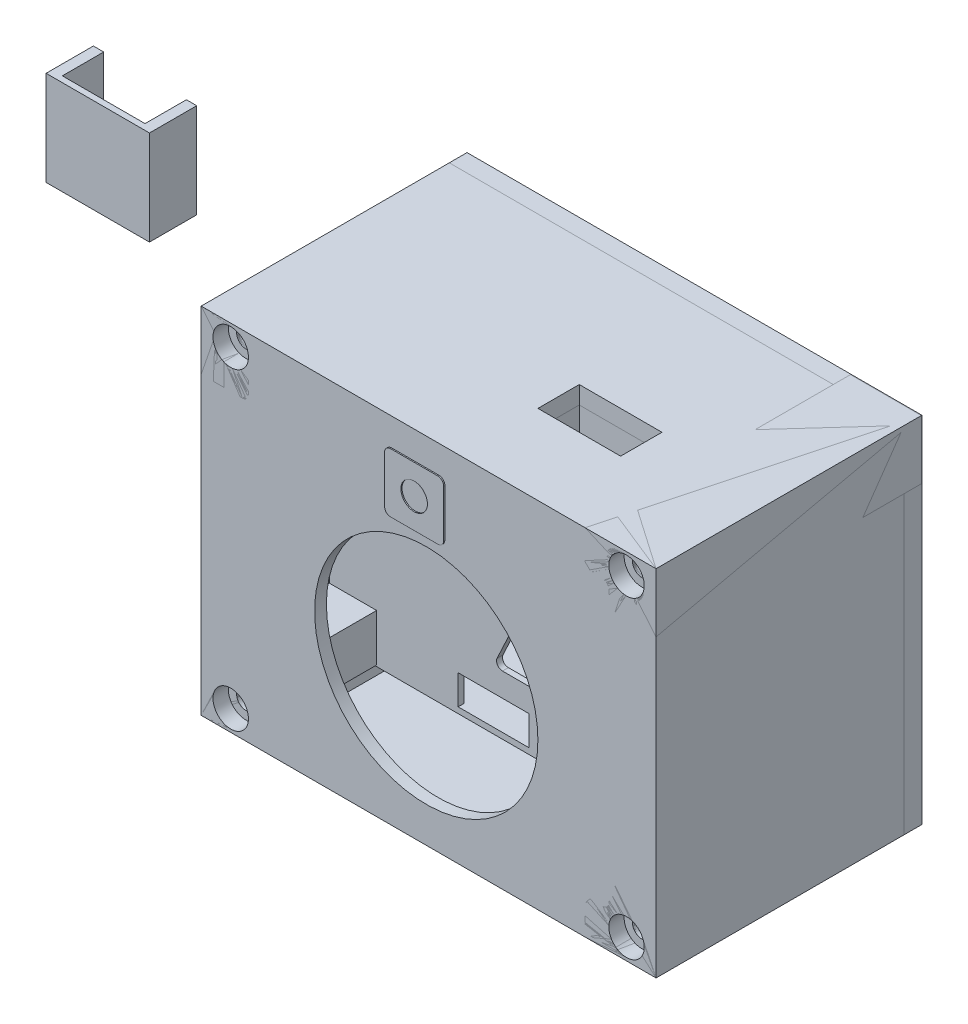
SolidWorks part; units mm, degrees
ref_plane "Front Plane" through (0, 0, 0) normal (0, 0, 1) x (1, 0, 0)
ref_plane "Top Plane" through (0, 0, 0) normal (0, 1, 0) x (1, 0, 0)
ref_plane "Right Plane" through (0, 0, 0) normal (1, 0, 0) x (0, 0, -1)
sketch "NodeBaseSection" plane through (0, 0, 0) normal (0, 0, 1) x (1, 0, 0)
  line L1 (0, 0) -> (-48.4, 0)
  line L2 (0, 0) -> (0, 25.7)
  line L3 (0, 25.7) -> (-48.4, 25.7)
  line L4 (-48.4, 0) -> (-48.4, 25.7)
  dimension "D1" = 48.4
  dimension "D2" = 25.7
sketch "WiFiModemSection" plane through (0, 0, 0) normal (0, 0, 1) x (1, 0, 0)
  line L1 (-7.6, 6.85) -> (-22.6, 6.85)
  line L2 (-7.6, 6.85) -> (-7.6, 18.85)
  line L3 (-7.6, 18.85) -> (-22.6, 18.85)
  line L4 (-22.6, 6.85) -> (-22.6, 18.85)
  line L5 (-49.2, 16.55) -> (-43.5, 16.55)
  line L6 (-49.2, 16.55) -> (-49.2, 9.15)
  line L7 (-49.2, 9.15) -> (-43.5, 9.15)
  line L8 (-43.5, 16.55) -> (-43.5, 9.15)
  dimension "D1" = 15
  dimension "D2" = 12
  dimension "D3" = 7.6
  dimension "D4" = 6.85
  dimension "D5" = 7.4
  dimension "D6" = 5.7
  dimension "D7" = 9.15
  dimension "D8" = 43.5
extrude "NodeBase" add sketch "NodeBaseSection" along normal blind 1.7 contours L3 L4 L1 L2
extrude "MicroPort+WiFiModem" add sketch "WiFiModemSection" along normal blind 2.7
sketch "AntennaSection" plane through (0, 0, 1.7) normal (0, 0, 1) x (1, 0, 0)
  line L0 (-6.6, 7.8) -> (-6.6, 18.2)
  line L1 (-6.6, 18.2) -> (-0.8, 18.2)
  line L2 (-0.8, 18.2) -> (-0.8, 15.8)
  line L3 (-0.8, 15.8) -> (-4.442, 15.8)
  line L4 (-4.442, 15.8) -> (-4.442, 15)
  line L5 (-4.442, 15) -> (-0.8, 15)
  line L6 (-0.8, 15) -> (-0.8, 12.6)
  line L7 (-0.8, 12.6) -> (-4.442, 12.6)
  line L8 (-4.442, 12.6) -> (-4.442, 11.8)
  line L9 (-4.442, 11.8) -> (-0.8, 11.8)
  line L10 (-0.8, 11.8) -> (-0.8, 9.4)
  line L11 (-0.8, 9.4) -> (-4.442, 9.4)
  line L12 (-4.442, 9.4) -> (-4.442, 8.6)
  line L13 (-4.442, 8.6) -> (-0.8, 8.6)
  line L14 (-0.8, 8.6) -> (-0.8, 4.6)
  line L15 (-0.8, 4.6) -> (-1.6, 4.6)
  line L16 (-1.6, 4.6) -> (-1.6, 7.8)
  line L17 (-1.6, 7.8) -> (-5.242, 7.8)
  line L18 (-5.242, 7.8) -> (-5.242, 10.2)
  line L19 (-5.242, 10.2) -> (-1.6, 10.2)
  line L20 (-1.6, 10.2) -> (-1.6, 11)
  line L21 (-1.6, 11) -> (-5.242, 11)
  line L22 (-5.242, 11) -> (-5.242, 13.4)
  line L23 (-5.242, 13.4) -> (-1.6, 13.4)
  line L24 (-1.6, 13.4) -> (-1.6, 14.2)
  line L25 (-1.6, 14.2) -> (-5.242, 14.2)
  line L26 (-5.242, 14.2) -> (-5.242, 16.6)
  line L27 (-5.242, 16.6) -> (-1.6, 16.6)
  line L28 (-1.6, 16.6) -> (-1.6, 17.4)
  line L29 (-1.6, 17.4) -> (-5.8, 17.4)
  line L30 (-5.8, 17.4) -> (-5.8, 7.8)
  line L31 (-5.8, 7.8) -> (-6.6, 7.8)
  dimension "D1" = 0.8
  dimension "D2" = 0.8
  dimension "D3" = 0.8
  dimension "D4" = 0.8
  dimension "D5" = 0.8
  dimension "D6" = 0.8
  dimension "D7" = 0.8
  dimension "D8" = 0.8
  dimension "D9" = 0.8
  dimension "D10" = 0.8
  dimension "D11" = 0.8
  dimension "D12" = 0.8
  dimension "D13" = 0.8
  dimension "D14" = 0.8
  dimension "D15" = 0.8
  dimension "D16" = 0.8
  dimension "D17" = 0.8
  dimension "D18" = 0.8
  dimension "D19" = 0.8
  dimension "D20" = 3.2
extrude "Antenna" add sketch "AntennaSection" along normal blind 0.2
move or copy body "MovedWholeNode" bodies to move or copy 112 copy no translate (72.4, -2.35, 0)
sketch "4NodeAttachmentHolesSection" plane through (0, 0, 0) normal (0, 0, -1) x (-1, 0, 0)
  line L0 (-72.4, -2.35) -> (-24, -2.35) construction
  circle A0 centre (-69.9, 0.05) radius 1.5
  circle A1 centre (-69.9, 20.95) radius 1.5
  circle A2 centre (-26.1, 20.95) radius 1.5
  circle A3 centre (-26.1, 0.05) radius 1.5
  dimension "D1" = 3
  dimension "D2" = 3
  dimension "D3" = 3
  dimension "D4" = 3
  dimension "D5" = 43.8
  dimension "D6" = 20.9
  dimension "D7" = 2.4
  dimension "D8" = 43.8
  dimension "D9" = 26.1
extrude "4NodeAttachmentHoles" cut sketch "4NodeAttachmentHolesSection" against normal blind 2
sketch "DSMBluePinsSection" plane through (0, 0, 0) normal (0, 0, 1) x (1, 0, 0)
  line L5 (-20.5, 43.05) -> (-14.5, 43.05)
  line L6 (-20.5, 43.05) -> (-20.5, 37.05)
  line L7 (-20.5, 37.05) -> (-14.5, 37.05)
  line L8 (-14.5, 43.05) -> (-14.5, 37.05)
  line L9 (-10.5, 43.05) -> (-4.5, 43.05)
  line L10 (-10.5, 43.05) -> (-10.5, 37.05)
  line L11 (-10.5, 37.05) -> (-4.5, 37.05)
  line L12 (-4.5, 43.05) -> (-4.5, 37.05)
  dimension "D3" = 6
  dimension "D4" = 6
  dimension "D5" = 6
extrude "DSMBluePins" add sketch "DSMBluePinsSection" along normal blind 5 contours L8 L7 L6 L5 | L11 L12 L9 L10
sketch "PCBSection" plane through (0, 0, 0) normal (0, 0, 1) x (1, 0, 0)
  line L1 (0, 0) -> (-58.8, 0)
  line L2 (0, 0) -> (0, 44.55)
  line L3 (0, 44.55) -> (-58.8, 44.55)
  line L4 (-58.8, 0) -> (-58.8, 44.55)
  dimension "D1" = 58.8
  dimension "D2" = 44.55
extrude "PCB" add sketch "PCBSection" against normal blind 1.5
sketch "BlackPlasticCoverSection" plane through (0, 0, 0) normal (0, 0, 1) x (1, 0, 0)
  line L0 (-58.8, 44.55) -> (-58.8, 0) construction
  line L5 (0, 1) -> (-58.8, 1)
  line L8 (-58.8, 1) -> (-58.8, 36.5)
  line L9 (0, -1.485) -> (0, 1.485) construction
  line L10 (0, 36.5) -> (-36.6, 36.5)
  line L11 (-36.6, 36.5) -> (-50.5, 43.3)
  line L12 (-50.5, 43.3) -> (-58.8, 36.5)
  line L13 (0, 7) -> (0, 1)
  line L14 (0, 7) -> (-2, 7)
  line L15 (-2, 7) -> (-2, 8)
  line L16 (-2, 8) -> (-4.5, 8)
  line L17 (-4.5, 8) -> (-4.5, 13)
  line L18 (-4.5, 13) -> (0, 13)
  line L19 (0, 13) -> (0, 36.5)
  dimension "D1" = 1
  dimension "D2" = 36.5
  dimension "D3" = 2
  dimension "D4" = 1
  dimension "D5" = 2.5
  dimension "D6" = 5
extrude "BlackPlasticCover" add sketch "BlackPlasticCoverSection" along normal blind 15 separate body
sketch "3HolesCutterSection" plane through (0, 0, 15) normal (0, 0, 1) x (1, 0, 0)
  line L0 (-6.5, 17) -> (-11.6962, 14)
  line L1 (-25, 2) -> (-37, 2)
  line L2 (-25, 2) -> (-25, 7)
  line L3 (-25, 7) -> (-37, 7)
  line L4 (-37, 2) -> (-37, 7)
  line L5 (-11.6962, 14) -> (-13.9462, 17.8971)
  line L6 (-13.9462, 17.8971) -> (-8.75, 20.8971)
  line L7 (-8.75, 20.8971) -> (-6.5, 17)
  line L8 (-21, 11) -> (-29.5, 11)
  line L9 (-30.4061, 12.4231) -> (-24.9061, 24.2023)
  line L10 (-24, 24.7792) -> (-21, 24.7792)
  line L11 (-20, 23.7792) -> (-20, 12)
  line L12 (21.45, 0) -> (-21.45, 0) construction
  arc A0 (-29.5, 11) -> (-30.4061, 12.4231) centre (-29.5, 12) cw
  arc A1 (-24.9061, 24.2023) -> (-24, 24.7792) centre (-24, 23.7792) cw
  arc A2 (-21, 24.7792) -> (-20, 23.7792) centre (-21, 23.7792) cw
  arc A3 (-21, 11) -> (-20, 12) centre (-21, 12) ccw
  dimension "D5" = 1
  dimension "D7" = 3
  dimension "D1" = 12
  dimension "D2" = 5
  dimension "D3" = 6
  dimension "D4" = 4.5
  dimension "D6" = 8.5
  dimension "D8" = 13
  dimension "D9" = 30
  dimension "D10" = 6.5
  dimension "D11" = 17
  dimension "D12" = 25
  dimension "D13" = 2
  dimension "D14" = 20
  dimension "D15" = 11
sketch "HoleCutterSection" [suppressed] plane through (0, 0, 0) normal (0, 0, 1) x (1, 0, 0)
  circle A0 centre (-31.75, 41.1) radius 2.25
  dimension "D1" = 4.5
  dimension "D2" = 27.05
extrude "HoleCutter" [suppressed] cut sketch "HoleCutterSection" against normal blind 3.2
shell "BlackDSMShell" thickness 1
sketch "SideHoleCutterSection" plane through (0, 36.5, 0) normal (0, 1, 0) x (1, 0, 0)
  line L1 (-10.5, -14) -> (-24.5, -14)
  line L2 (-10.5, -14) -> (-10.5, -7)
  line L3 (-10.5, -7) -> (-24.5, -7)
  line L4 (-24.5, -14) -> (-24.5, -7)
  dimension "D1" = 7
  dimension "D2" = 14
  dimension "D3" = 10.5
  dimension "D4" = 14
extrude "SideHoleCutter" cut sketch "SideHoleCutterSection" against normal blind 1.5 contours L1 L4 L3 L2
extrude "3HolesCutter" cut sketch "3HolesCutterSection" against normal blind 1.5
sketch "5PinConnectorHoleCutterSection" [suppressed] plane through (0, 1, 0) normal (0, -1, 0) x (1, 0, 0)
  line L1 (-57.8, 0) -> (-37.8, 0)
  line L2 (-57.8, 0) -> (-57.8, 11)
  line L3 (-57.8, 11) -> (-37.8, 11)
  line L4 (-37.8, 0) -> (-37.8, 11)
  line L6 (-58.8, 15) -> (-58.8, 0) construction
  dimension "D1" = 11
  dimension "D2" = 20
  dimension "D3" = 1
  dimension "D4" = 0
extrude "5PinConnectorHoleCutter" [suppressed] cut sketch "5PinConnectorHoleCutterSection" against normal blind 1.5
sketch "5PinConnectorSection" [suppressed] plane through (0, 0, 0) normal (0, 0, 1) x (1, 0, 0)
  line L1 (-54.7, 15.6) -> (-42.7, 15.6)
  line L2 (-54.7, 15.6) -> (-54.7, 2.6)
  line L3 (-54.7, 2.6) -> (-42.7, 2.6)
  line L4 (-42.7, 15.6) -> (-42.7, 2.6)
  dimension "D1" = 12
  dimension "D2" = 13
extrude "5PinConnector" [suppressed] add sketch "5PinConnectorSection" along normal blind 5 contours L1 L4 L3 L2
shell "WhiteConnectorShell" [suppressed] thickness 0.5
sketch "BoxCapSection(ToNode)" plane through (0, 0, 0) normal (0, 0, 1) x (1, 0, 0)
  line L1 (21, -19.5) -> (98, -19.5)
  line L2 (21, -19.5) -> (21, 40.5)
  line L3 (21, 40.5) -> (98, 40.5)
  line L4 (98, -19.5) -> (98, 40.5)
  line L5 (-14.8, 82.1) -> (62.2, 82.1) construction
  line L6 (-14.8, 82.1) -> (-14.8, 132.1) construction
  line L7 (-14.8, 132.1) -> (62.2, 132.1) construction
  line L8 (62.2, 82.1) -> (62.2, 132.1) construction
  circle A0 centre (-9.8, 127.1) radius 1.5
  circle A1 centre (57.2, 87.1) radius 1.5
  dimension "D6" = 3
  dimension "D7" = 3
  dimension "D1" = 60
  dimension "D2" = 77
  dimension "D3" = 50
  dimension "D5" = 77
  dimension "D8" = 5
  dimension "D9" = 5
  dimension "D10" = 5
  dimension "D11" = 5
extrude "BoxCap(ToNode)" add sketch "BoxCapSection(ToNode)" along normal blind 3 from offset 9 separate body contours L1 L4 L3 L2 offset against normal yes
sketch "NodeScrewColumnsSection" plane through (0, 0, -6) normal (0, 0, 1) x (1, 0, 0)
  line L1 (64.4, -2.15) -> (72.4, -2.15)
  line L2 (64.4, -2.15) -> (64.4, 5.85)
  line L3 (64.4, 5.85) -> (72.4, 5.85)
  line L4 (72.4, -2.15) -> (72.4, 5.85)
  line L28 (24, -2.15) -> (32, -2.15)
  line L29 (24, -2.15) -> (24, 5.85)
  line L30 (24, 5.85) -> (32, 5.85)
  line L31 (32, -2.15) -> (32, 5.85)
  line L32 (24, 15) -> (32, 15)
  line L33 (24, 15) -> (24, 23)
  line L34 (24, 23) -> (32, 23)
  line L35 (32, 15) -> (32, 23)
  line L36 (64.4, 15) -> (72.4, 15)
  line L37 (64.4, 15) -> (64.4, 23)
  line L38 (64.4, 23) -> (72.4, 23)
  line L39 (72.4, 15) -> (72.4, 23)
  dimension "D1" = 8
  dimension "D2" = 8
  dimension "D3" = 8
  dimension "D4" = 8
  dimension "D5" = 8
  dimension "D6" = 8
  dimension "D7" = 8
  dimension "D8" = 8
  dimension "D9" = 24
  dimension "D10" = 2.15
  dimension "D11" = 24
  dimension "D12" = 15
  dimension "D13" = 72.4
  dimension "D14" = 2.15
  dimension "D15" = 72.4
  dimension "D16" = 15
extrude "NodeScrewColumns" add sketch "NodeScrewColumnsSection" along normal blind 6
sketch "BoxCapSection(ToDSM)" plane through (0, 0, 0) normal (0, 0, 1) x (1, 0, 0)
  line L0 (21, -19.5) -> (98, -19.5)
  line L1 (21, -19.5) -> (21, 40.5)
  line L2 (21, 40.5) -> (98, 40.5)
  line L3 (98, -19.5) -> (98, 40.5)
  line L4 (-23.4569, 88.0645) -> (53.5431, 88.0645) construction
  line L5 (-23.4569, 88.0645) -> (-23.4569, 138.0645) construction
  line L6 (-23.4569, 138.0645) -> (53.5431, 138.0645) construction
  line L7 (53.5431, 88.0645) -> (53.5431, 138.0645) construction
  circle A0 centre (-18.4569, 133.0645) radius 1.5
  circle A1 centre (48.5431, 93.0645) radius 1.5
  dimension "D1" = 77
  dimension "D2" = 60
extrude "BoxCap(ToDSM)" add sketch "BoxCapSection(ToDSM)" against normal blind 42 from offset 36 separate body contours L0 L3 L2 L1
shell "HollowBoxCap(ToDSM)" thickness 3
sketch "DSMLegsSection" plane through (0, 0, 33) normal (0, 0, -1) x (-1, 0, 0)
  line L1 (-88.9, -9.77) -> (-30.2, -9.77) construction
  line L2 (-88.9, -9.77) -> (-88.9, 25.5) construction
  line L3 (-88.9, 25.5) -> (-30.2, 25.5) construction
  line L4 (-30.2, -9.77) -> (-30.2, 25.5) construction
  line L6 (-24, -16.5) -> (-95, -16.5) construction
  line L7 (-95, -16.5) -> (-95, 37.5) construction
  line L9 (-30.2, -9.77) -> (-38.2, -9.77)
  line L10 (-30.2, -9.77) -> (-30.2, -1.77)
  line L11 (-30.2, -1.77) -> (-38.2, -1.77)
  line L12 (-38.2, -9.77) -> (-38.2, -1.77)
  line L13 (-30.2, 17.5) -> (-38.2, 17.5)
  line L14 (-30.2, 17.5) -> (-30.2, 25.5)
  line L15 (-30.2, 25.5) -> (-38.2, 25.5)
  line L16 (-38.2, 17.5) -> (-38.2, 25.5)
  line L17 (-80.9, -9.77) -> (-88.9, -9.77)
  line L18 (-80.9, -9.77) -> (-80.9, -4.27)
  line L19 (-80.9, -4.27) -> (-88.9, -4.27)
  line L20 (-88.9, -9.77) -> (-88.9, -4.27)
  line L21 (-80.9, 17.5) -> (-88.9, 17.5)
  line L22 (-80.9, 17.5) -> (-80.9, 25.5)
  line L23 (-80.9, 25.5) -> (-88.9, 25.5)
  line L24 (-88.9, 17.5) -> (-88.9, 25.5)
  dimension "D13" = 30.2
  dimension "D2" = 25.5
  dimension "D3" = 6.73
  dimension "D4" = 6.1
  dimension "D5" = 8
  dimension "D6" = 8
  dimension "D7" = 8
  dimension "D8" = 8
  dimension "D9" = 5.5
  dimension "D10" = 8
  dimension "D11" = 8
  dimension "D12" = 8
extrude "DSMLegs" add sketch "DSMLegsSection" along normal blind 9.5
sketch "FanCutterSection" plane through (0, 0, 36) normal (0, 0, 1) x (1, 0, 0)
  circle A4 centre (59.1, 5.4) radius 18.9
  point P12 (79.2, 28.2)
  point P15 (79.2, -12)
  point P18 (39, 28.2)
  dimension "D3" = 59.1
  dimension "D6" = 37.8
  dimension "D1" = 40.2
  dimension "D2" = 40.2
  dimension "D4" = 5.4
sketch "SquareFanBodyCutterSection" plane through (0, 0, 36) normal (0, 0, 1) x (1, 0, 0)
  line L0 (42.1, -14.6) -> (76.1, -14.6)
  line L1 (39.1, -11.6) -> (39.1, 22.4)
  line L2 (42.1, 25.4) -> (76.1, 25.4)
  line L3 (79.1, -11.6) -> (79.1, 22.4)
  line L4 (42.1, -11.6) -> (76.1, 22.4) construction
  line L5 (42.1, 22.4) -> (76.1, -11.6) construction
  arc A0 (42.1, -14.6) -> (39.1, -11.6) centre (42.1, -11.6) cw
  arc A1 (76.1, 25.4) -> (79.1, 22.4) centre (76.1, 22.4) cw
  arc A2 (76.1, -14.6) -> (79.1, -11.6) centre (76.1, -11.6) ccw
  arc A3 (39.1, 22.4) -> (42.1, 25.4) centre (42.1, 22.4) cw
  dimension "D1" = 3
  dimension "D3" = 34
  dimension "D4" = 34
extrude "FanCutter" cut sketch "FanCutterSection" against normal blind 3
extrude "SquareFanBodyCutter" cut sketch "SquareFanBodyCutterSection" against normal blind 3 from offset 2 offset against normal yes
sketch "ExhaustDuctSection" plane through (0, 40.5, 0) normal (0, 1, 0) x (1, 0, 0)
  line L0 (-10.5, -7) -> (-8.75, -7)
  line L1 (-8.75, -7) -> (-8.75, -15)
  line L2 (-8.75, -15) -> (-26.25, -15)
  line L3 (0, -15) -> (-36.6, -15) construction
  line L4 (-26.25, -15) -> (-26.25, -7)
  line L5 (-26.25, -7) -> (-24.5, -7)
  line L6 (-24.5, -7) -> (-24.5, -14)
  line L7 (-24.5, -14) -> (-24.5, -7) construction
  line L8 (-24.5, -14) -> (-10.5, -14)
  line L9 (-10.5, -14) -> (-10.5, -7) construction
  line L10 (-25, -14) -> (-1, -14) construction
  line L11 (-10.5, -14) -> (-10.5, -7)
  dimension "D1" = 1.75
extrude "ExhaustDuct" add sketch "ExhaustDuctSection" against normal blind 16 separate body
sketch "ExhaustHoleCutterSection" plane through (0, 40.5, 0) normal (0, 1, 0) x (1, 0, 0)
  line L1 (78.5, -22.5) -> (64.5, -22.5)
  line L2 (78.5, -22.5) -> (78.5, -15.5)
  line L3 (78.5, -15.5) -> (64.5, -15.5)
  line L4 (64.5, -22.5) -> (64.5, -15.5)
  dimension "D1" = 14
  dimension "D2" = 7
  dimension "D3" = 64.5
  dimension "D4" = 15.5
extrude "ExhaustHoleCutter" cut sketch "ExhaustHoleCutterSection" against normal blind 5
sketch "MicroUSBHoleCutterSection" plane through (21, 0, 0) normal (-1, 0, 0) x (0, 0, 1)
  line L1 (3.6, 16.75) -> (-0.9, 16.75)
  line L2 (4.6, 15.75) -> (4.6, 5.25)
  line L3 (3.6, 4.25) -> (-0.9, 4.25)
  line L4 (-1.9, 15.75) -> (-1.9, 5.25)
  arc A0 (4.6, 5.25) -> (3.6, 4.25) centre (3.6, 5.25) cw
  arc A1 (-0.9, 4.25) -> (-1.9, 5.25) centre (-0.9, 5.25) cw
  arc A2 (-0.9, 16.75) -> (-1.9, 15.75) centre (-0.9, 15.75) ccw
  arc A3 (3.6, 16.75) -> (4.6, 15.75) centre (3.6, 15.75) cw
  point P10 (4.6, 4.25)
  point P13 (-1.9, 4.25)
  point P18 (4.6, 16.75)
  dimension "D5" = 1
  dimension "D1" = 12.5
  dimension "D2" = 6.5
  dimension "D3" = 4.25
  dimension "D4" = 4.6
move or copy body "DSMModule" bodies to move or copy 116 106 copy no translate (89, -11, 8.5)
sketch "ScrewDSMHoleCutterSection" plane through (0, 0, 8.5) normal (0, 0, 1) x (1, 0, 0)
  line L0 (30.2, 33.55) -> (30.2, -11) construction
  circle A0 centre (57.25, 30.825) radius 2.25
  dimension "D2" = 4.5
  dimension "D1" = 27.05
  dimension "D3" = 30.825
extrude "ScrewDSMHoleCutter" cut sketch "ScrewDSMHoleCutterSection" against normal blind 2
extrude "MicroUSBHoleCutter" cut sketch "MicroUSBHoleCutterSection" against normal blind 3 contours L3 A1 L4 A2 L1 A3 L2 A0
sketch "ExhaustHoleDuctSection" plane through (0, 25.5, 0) normal (0, 1, 0) x (1, 0, 0)
  line L16 (79.5, -23.5) -> (63.5, -23.5)
  line L17 (78.5, -22.5) -> (64.5, -22.5)
  line L18 (78.5, -22.5) -> (78.5, -15.5)
  line L19 (78.5, -15.5) -> (64.5, -15.5)
  line L20 (64.5, -22.5) -> (64.5, -15.5)
  line L21 (63.5, -23.5) -> (63.5, -14.5)
  line L22 (79.5, -14.5) -> (63.5, -14.5)
  line L23 (79.5, -23.5) -> (79.5, -14.5)
  line M13 (64.5, -15.5) -> (78.5, -15.5)
  line M14 (78.5, -15.5) -> (78.5, -22.5)
  line M15 (78.5, -22.5) -> (64.5, -22.5)
  line M16 (64.5, -22.5) -> (64.5, -15.5)
  line M19 (52.4, -23.5) -> (89, -23.5)
  dimension "D1" = 1
extrude "ExhaustHoleDuct" add sketch "ExhaustHoleDuctSection" along normal blind 12 separate body contours L23 L22 L21 M19 M16 M13 M14 M15
sketch "DSMPCBScrewHoleSection" plane through (0, 0, 8.5) normal (0, 0, 1) x (1, 0, 0)
  line L1 (61.25, 25.825) -> (53.25, 25.825)
  line L2 (62.25, 26.825) -> (62.25, 34.825)
  line L3 (61.25, 35.825) -> (53.25, 35.825)
  line L4 (52.25, 26.825) -> (52.25, 34.825)
  circle A0 centre (57.25, 30.825) radius 2.25
  arc A1 (62.25, 34.825) -> (61.25, 35.825) centre (61.25, 34.825) ccw
  arc A2 (61.25, 25.825) -> (62.25, 26.825) centre (61.25, 26.825) ccw
  arc A3 (53.25, 25.825) -> (52.25, 26.825) centre (53.25, 26.825) cw
  arc A4 (53.25, 35.825) -> (52.25, 34.825) centre (53.25, 34.825) ccw
  point P9 (62.25, 35.825)
  point P12 (62.25, 25.825)
  point P15 (52.25, 25.825)
  circle M4 centre (57.25, 30.825) radius 2.25
  line M10 (89, 33.55) -> (30.2, 33.55)
  dimension "D5" = 4.5
  dimension "D6" = 1
  dimension "D1" = 10
  dimension "D2" = 10
  dimension "D3" = 5
  dimension "D4" = 5
extrude "DSMPCBScrewHole" add sketch "DSMPCBScrewHoleSection" along normal blind 27.7 separate body contours L3 A4 L4 L2 A1 M10 | A3 L1 A2 L2 L4 M10 M4 | A0
sketch "DSMPCBScrewHoleAdditionalSection" plane through (0, 0, 8.5) normal (0, 0, -1) x (-1, 0, 0)
  line L0 (-62.25, 26.825) -> (-62.25, 34.825) construction
  line L1 (-62.25, 33.55) -> (-52.25, 33.55)
  line L2 (-62.25, 33.55) -> (-62.25, 34.825)
  line L3 (-61.25, 35.825) -> (-53.25, 35.825)
  line L4 (-52.25, 33.55) -> (-52.25, 34.825)
  line L5 (-89, 33.55) -> (-30.2, 33.55) construction
  arc A0 (-53.25, 35.825) -> (-52.25, 34.825) centre (-53.25, 34.825) cw
  arc A1 (-62.25, 34.825) -> (-61.25, 35.825) centre (-61.25, 34.825) cw
  dimension "D2" = 1
  dimension "D1" = 10
  dimension "D3" = 35.825
extrude "DSMPCBScrewHoleAdditional" add sketch "DSMPCBScrewHoleAdditionalSection" along normal blind 1.5 contours L3 A0 L4 L1 L2 A1
sketch "BoxClosingScrewColumnsSection" plane through (0, 0, 36) normal (0, 0, 1) x (1, 0, 0)
  line L0 (21, 30.5) -> (21, 40.5)
  line L1 (21, -19.5) -> (21, 40.5) construction
  line L2 (21, 40.5) -> (33, 40.5)
  line L3 (21, 40.5) -> (98, 40.5) construction
  line L4 (21, 30.5) -> (28, 30.5)
  line L5 (29, 31.5) -> (29, 33.5)
  line L6 (30, 34.5) -> (32, 34.5)
  line L7 (33, 35.5) -> (33, 40.5)
  line L8 (21, -19.5) -> (21, 40.5) construction
  line L9 (21, 40.5) -> (98, 40.5) construction
  line L10 (98, 30.5) -> (98, 40.5)
  line L11 (98, -19.5) -> (98, 40.5) construction
  line L12 (98, 40.5) -> (86, 40.5)
  line L13 (86, 40.5) -> (86, 35.5)
  line L14 (87, 34.5) -> (89, 34.5)
  line L15 (90, 33.5) -> (90, 31.5)
  line L16 (91, 30.5) -> (98, 30.5)
  line L17 (188.9609, 10.5) -> (7.0391, 10.5) construction
  line L19 (91, -9.5) -> (98, -9.5)
  line L20 (90, -12.5) -> (90, -10.5)
  line L21 (87, -13.5) -> (89, -13.5)
  line L22 (86, -19.5) -> (86, -14.5)
  line L23 (98, -19.5) -> (86, -19.5)
  line L24 (98, -9.5) -> (98, -19.5)
  line L25 (33, -14.5) -> (33, -19.5)
  line L26 (30, -13.5) -> (32, -13.5)
  line L27 (29, -10.5) -> (29, -12.5)
  line L28 (21, -9.5) -> (28, -9.5)
  line L29 (21, -19.5) -> (33, -19.5)
  line L30 (21, -9.5) -> (21, -19.5)
  arc A0 (32, 34.5) -> (33, 35.5) centre (32, 35.5) ccw
  arc A1 (28, 30.5) -> (29, 31.5) centre (28, 31.5) ccw
  arc A2 (29, 33.5) -> (30, 34.5) centre (30, 33.5) cw
  arc A3 (86, 35.5) -> (87, 34.5) centre (87, 35.5) ccw
  arc A4 (89, 34.5) -> (90, 33.5) centre (89, 33.5) cw
  arc A5 (90, 31.5) -> (91, 30.5) centre (91, 31.5) ccw
  arc A6 (90, -10.5) -> (91, -9.5) centre (91, -10.5) cw
  arc A7 (89, -13.5) -> (90, -12.5) centre (89, -12.5) ccw
  arc A8 (86, -14.5) -> (87, -13.5) centre (87, -14.5) cw
  arc A9 (29, -12.5) -> (30, -13.5) centre (30, -12.5) ccw
  arc A10 (28, -9.5) -> (29, -10.5) centre (28, -10.5) cw
  arc A11 (32, -13.5) -> (33, -14.5) centre (32, -14.5) cw
  dimension "D1" = 1
  dimension "D8" = 1
  dimension "D2" = 7
  dimension "D3" = 5
  dimension "D4" = 12
  dimension "D5" = 10
  dimension "D6" = 10
  dimension "D7" = 12
  dimension "D9" = 7
  dimension "D10" = 5
extrude "BoxClosingScrewColumns" add sketch "BoxClosingScrewColumnsSection" against normal blind 44.9 separate body
sketch "BoxClosingScrewHolesCutterSection" plane through (0, 0, 36) normal (0, 0, 1) x (1, 0, 0)
  line L6 (158.4, 10.5) -> (150.0185, 10.5) construction
  line L7 (98, -19.5) -> (98, 40.5) construction
  circle A0 centre (26, 37) radius 1.6
  circle A1 centre (93, 37) radius 1.6
  circle A2 centre (93, -16) radius 1.6
  circle A3 centre (26, -16) radius 1.6
  point P9 (98, 10.5)
  dimension "D1" = 3.2
  dimension "D4" = 3.2
  dimension "D2" = 37
  dimension "D3" = 26
  dimension "D5" = 93
  dimension "D6" = 37
extrude "BoxClosingScrewHolesCutter" cut sketch "BoxClosingScrewHolesCutterSection" against normal blind 45.9
sketch "NutCutterSection" plane through (0, 0, -9) normal (0, 0, -1) x (-1, 0, 0)
  line L0 (-21, 40.5) -> (-98, 40.5) construction
  line L1 (-27.6166, 34.2) -> (-24.3834, 34.2)
  line L2 (-24.3834, 34.2) -> (-22.7668, 37)
  line L3 (-22.7668, 37) -> (-24.3834, 39.8)
  line L4 (-24.3834, 39.8) -> (-27.6166, 39.8)
  line L5 (-27.6166, 39.8) -> (-29.2332, 37)
  line L6 (-29.2332, 37) -> (-27.6166, 34.2)
  line L7 (-153, 10.5) -> (-114.9089, 10.5) construction
  line L8 (-89.7668, 37) -> (-91.3834, 39.8)
  line L9 (-91.3834, 39.8) -> (-94.6166, 39.8)
  line L10 (-94.6166, 39.8) -> (-96.2332, 37)
  line L11 (-96.2332, 37) -> (-94.6166, 34.2)
  line L12 (-94.6166, 34.2) -> (-91.3834, 34.2)
  line L13 (-91.3834, 34.2) -> (-89.7668, 37)
  line L14 (-98, -19.5) -> (-98, 40.5) construction
  line L15 (-91.3834, -13.2) -> (-89.7668, -16)
  line L16 (-94.6166, -13.2) -> (-91.3834, -13.2)
  line L17 (-96.2332, -16) -> (-94.6166, -13.2)
  line L18 (-94.6166, -18.8) -> (-96.2332, -16)
  line L19 (-91.3834, -18.8) -> (-94.6166, -18.8)
  line L20 (-89.7668, -16) -> (-91.3834, -18.8)
  line L21 (-29.2332, -16) -> (-27.6166, -13.2)
  line L22 (-27.6166, -18.8) -> (-29.2332, -16)
  line L23 (-24.3834, -18.8) -> (-27.6166, -18.8)
  line L24 (-22.7668, -16) -> (-24.3834, -18.8)
  line L25 (-24.3834, -13.2) -> (-22.7668, -16)
  line L26 (-27.6166, -13.2) -> (-24.3834, -13.2)
  circle A0 centre (-26, 37) radius 2.8 construction
  circle A1 centre (-93, 37) radius 2.8 construction
  circle A2 centre (-93, -16) radius 2.8 construction
  circle A3 centre (-26, -16) radius 2.8 construction
  point P24 (-98, 10.5)
  dimension "D1" = 5.6
  dimension "D2" = 5.6
extrude "NutCutter" cut sketch "NutCutterSection" against normal blind 2.3
sketch "ScrewHeadBedCutterSection" plane through (0, 0, 36) normal (0, 0, 1) x (1, 0, 0)
  circle A0 centre (93, -16) radius 3
  circle A1 centre (26, -16) radius 3
  circle A2 centre (26, 37) radius 3
  circle A3 centre (93, 37) radius 3
  dimension "D1" = 6
  dimension "D2" = 6
  dimension "D3" = 6
  dimension "D4" = 6
extrude "ScrewHeadBedCutter" cut sketch "ScrewHeadBedCutterSection" against normal blind 2.6
